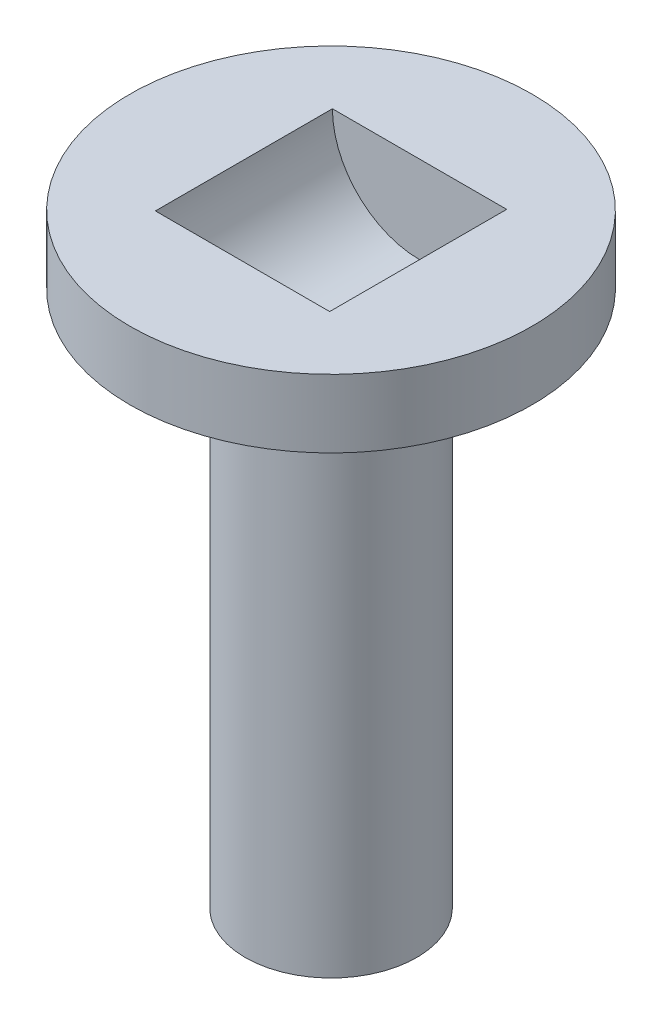
SolidWorks part; units mm, degrees
ref_plane "Front Plane" through (0, 0, 0) normal (0, 0, 1) x (1, 0, 0)
ref_plane "Top Plane" through (0, 0, 0) normal (0, 1, 0) x (1, 0, 0)
ref_plane "Right Plane" through (0, 0, 0) normal (1, 0, 0) x (0, 0, -1)
sketch "Sketch1" plane through (0, 0, 0) normal (0, 1, 0) x (1, 0, 0)
  circle A0 centre (0, 0) radius 3.2
  dimension "D1" = 6.4
extrude "Boss-Extrude1" add sketch "Sketch1" along normal blind 20
sketch "Sketch2" plane through (0, 0, 0) normal (0, -1, 0) x (1, 0, 0)
  circle A0 centre (0, 0) radius 1.1
  dimension "D1" = 2.2
extrude "Cut-Extrude1" cut sketch "Sketch2" against normal blind 10
sketch "Sketch4" plane through (0, 20, 0) normal (0, 1, 0) x (1, 0, 0)
  circle A0 centre (0, 0) radius 7.5
  dimension "D1" = 15
extrude "Boss-Extrude2" add sketch "Sketch4" along normal blind 2.54
sketch "Sketch6" plane through (0, 22.54, 0) normal (0, 1, 0) x (1, 0, 0)
  circle A0 centre (0, 0) radius 4.85
  dimension "D1" = 9.7
extrude "Boss-Extrude3" add sketch "Sketch6" against normal blind 3.35
sketch "Sketch5" plane through (0, 0, 0) normal (0, 0, 1) x (1, 0, 0)
  line L0 (7.5, 22.54) -> (-7.5, 22.54) construction
  circle A0 centre (0, 22.54) radius 3.25
  dimension "D1" = 6.5
extrude "Cut-Extrude3" cut sketch "Sketch5" against normal blind 3.302 and the other way blind 3.3
